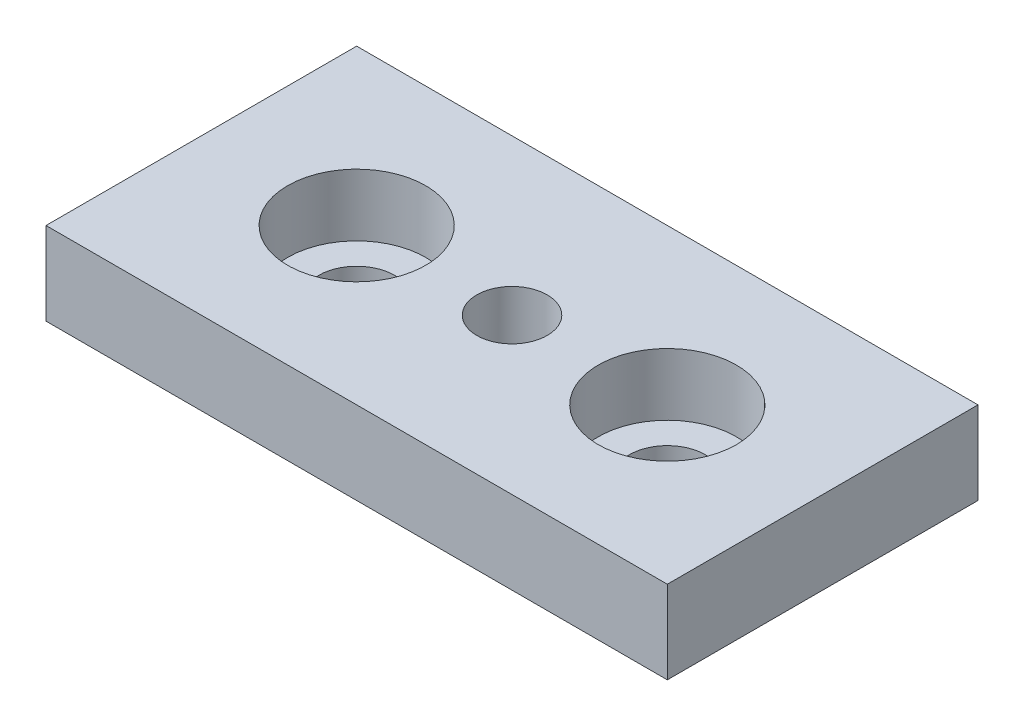
SolidWorks part; units mm, degrees
material "Алюминиевый сплав"
ref_plane "Спереди" through (0, 0, 0) normal (0, 0, 1) x (1, 0, 0)
ref_plane "Сверху" through (0, 0, 0) normal (0, 1, 0) x (1, 0, 0)
ref_plane "Справа" through (0, 0, 0) normal (1, 0, 0) x (0, 0, -1)
sketch "Эскиз1" plane through (0, 0, 0) normal (0, 1, 0) x (1, 0, 0)
  line L1 (-45, -22.5) -> (45, -22.5)
  line L2 (-45, -22.5) -> (-45, 22.5)
  line L3 (-45, 22.5) -> (45, 22.5)
  line L4 (45, -22.5) -> (45, 22.5)
  line L5 (-45, -22.5) -> (45, 22.5) construction
  line L6 (-45, 22.5) -> (45, -22.5) construction
  point P0 (0, 0)
  dimension "D1" = 90
  dimension "D2" = 45
extrude "Бобышка-Вытянуть1" add sketch "Эскиз1" along normal blind 12
sketch "Эскиз2" plane through (0, 0, 0) normal (0, 0, 1) x (1, 0, 0)
  line L0 (0, 0) -> (0, 12) construction
  line L1 (-45, 0) -> (45, 0) construction
  line L2 (-45, 12) -> (45, 12) construction
  line L3 (-32.5, 12) -> (-32.5, 3)
  line L4 (-32.5, 3) -> (-28, 3)
  line L5 (-28, 3) -> (-28, 0)
  line L6 (-28, 0) -> (-22.5, 0)
  line L7 (-22.5, 0) -> (-22.5, 12) construction
  line L8 (-22.5, 12) -> (-32.5, 12)
  line L9 (-22.5, 12) -> (-22.5, 0)
  dimension "D1" = 11
  dimension "D2" = 3
  dimension "D3" = 20
  dimension "D4" = 45
revolve "Вырез-Повернуть1" cut sketch "Эскиз2" angle 360 about L9
mirror "Зеркальное отражение1" about plane through (0, 0, 0) normal (1, 0, 0) of "Вырез-Повернуть1"
hole_wizard "Отверстие обработанное метчиком M121" positions "Эскиз3" profile "Эскиз5" tap size "M12" standard "ISO" end condition up to next
sketch "Эскиз3" plane through (0, 12, 0) normal (0, 1, 0) x (1, 0, 0)
  point P0 (0, 0)
sketch "Эскиз5" plane through (0, 12, 0) normal (1, 0, 0) x (0, 0, 1)
  line L0 (0, 0) -> (0, 12)
  line L1 (0, 12) -> (5.1, 12)
  line L2 (5.1, 12) -> (5.1, 0)
  line L5 (5.1, 0) -> (0, 0)
  line L11 (0, -6.35) -> (0, 107.95) construction
  dimension "Диаметр проходного сверла" = 10.2
  dimension "Глубина проходного сверла" = 12
cosmetic thread "Отверстие резьбы1" parameters "D2"=12
